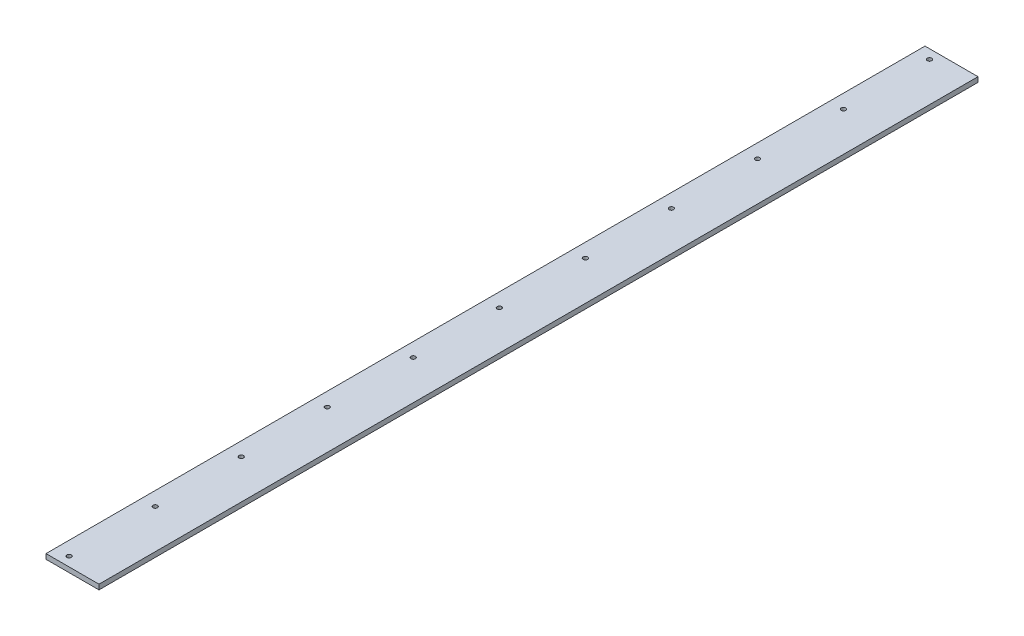
SolidWorks part; units mm, degrees
material "Неопрен"
ref_plane "Спереди" through (0, 0, 0) normal (0, 0, 1) x (1, 0, 0)
ref_plane "Сверху" through (0, 0, 0) normal (0, 1, 0) x (1, 0, 0)
ref_plane "Справа" through (0, 0, 0) normal (1, 0, 0) x (0, 0, -1)
sketch "Эскиз1" plane through (0, 0, 0) normal (0, 0, 1) x (1, 0, 0)
  line L0 (-69.3732, 0) -> (5, 0) construction
  line L1 (-32.1866, 0) -> (52.8134, 0)
  line L2 (-32.1866, 0) -> (-32.1866, 8)
  line L3 (-32.1866, 8) -> (52.8134, 8)
  line L4 (52.8134, 0) -> (52.8134, 8)
  dimension "D1" = 8
  dimension "D2" = 85
extrude "Бобышка-Вытянуть1" add sketch "Эскиз1" along normal offset from surface (705 mm away) 5
hole_wizard "Отверстие с зазором M6.51" positions "Эскиз2" profile "Эскиз3" hole size "M6.5" standard "ISO" end condition through all
sketch "Эскиз2" plane through (0, 0, 0) normal (0, -1, 0) x (-1, 0, 0)
  point P0 (10.0061, -690)
  point P3 (10.0061, -552)
  point P6 (10.0061, -414)
  point P9 (10.0061, -138)
  point P12 (10.0061, 0)
  point P16 (10.0061, -276)
sketch "Эскиз3" plane through (-10.0061, 0, 690) normal (1, 0, 0) x (0, 0, -1)
  line L0 (0, 0) -> (0, 8)
  line L1 (0, 8) -> (3.55, 8)
  line L2 (3.55, 8) -> (3.55, 0)
  line L5 (3.55, 0) -> (0, 0)
  line L11 (0, -6.35) -> (0, 107.95) construction
  dimension "Диаметр сквозного отверстия" = 7.1
  dimension "Глубина сквозного отверстия" = 8
mirror "Зеркальное отражение1" about plane through (0, 0, 0) normal (0, 0, -1) of bodies 104
